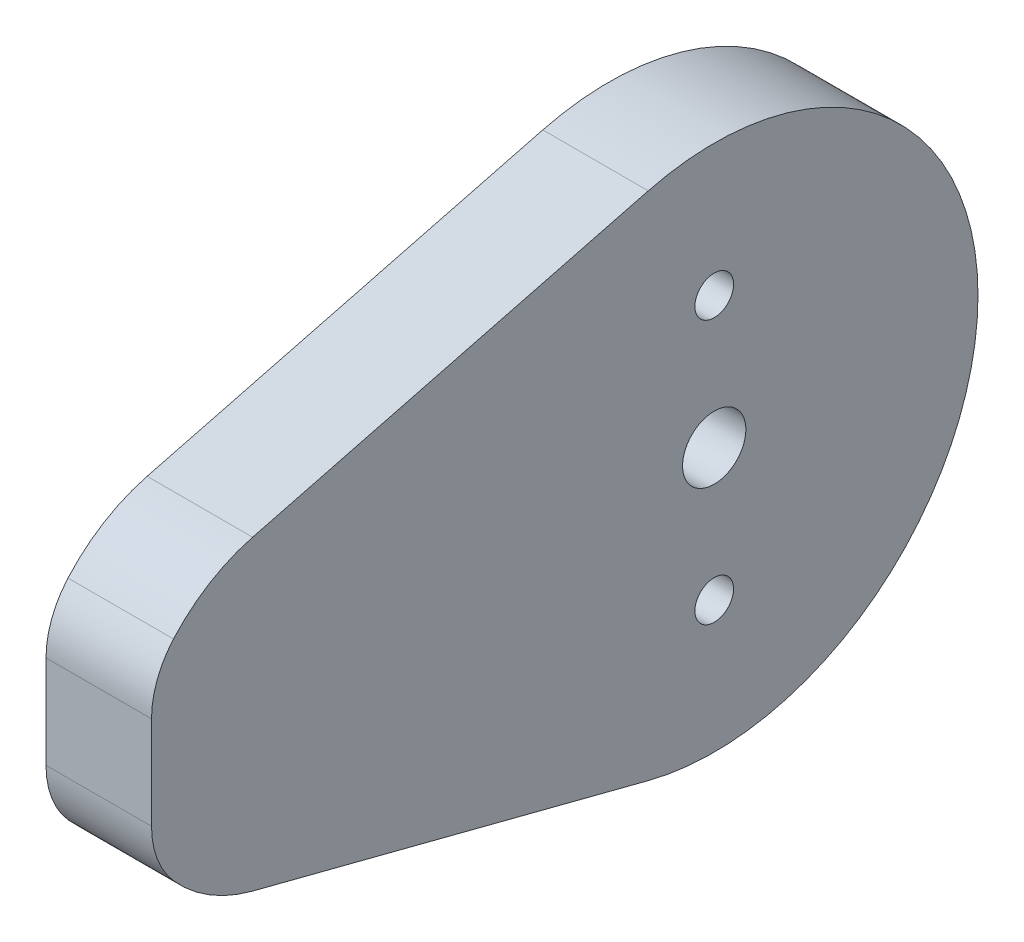
SolidWorks part; units mm, degrees
ref_plane "Plan de face" through (0, 0, 0) normal (0, 0, 1) x (1, 0, 0)
ref_plane "Plan de dessus" through (0, 0, 0) normal (0, 1, 0) x (1, 0, 0)
ref_plane "Plan de droite" through (0, 0, 0) normal (1, 0, 0) x (0, 0, -1)
sketch "Esquisse1" plane through (0, 0, 0) normal (1, 0, 0) x (0, 0, -1)
  line L0 (61.1, -8.9434) -> (61.1, 59.3647) construction
  line L1 (66.1354, 33.9) -> (52.8313, 33.9) construction
  line L2 (37.1, 3.4262) -> (37.1, 59.3647) construction
  line L3 (29.1, 44.0458) -> (29.1, 38.7542)
  line L4 (82, -8.9434) -> (82, 76.684) construction
  line L6 (34.85, 32.6858) -> (57.35, 26.8763)
  line L7 (94.833, 41.4) -> (22.7655, 41.4) construction
  line L8 (34.85, 50.1142) -> (57.35, 55.9237)
  line L26 (29.1, 58.1981) -> (29.1, -8.9434) construction
  circle A0 centre (61.1, 33.9) radius 1.1
  circle A1 centre (61.1, 48.9) radius 1.1
  arc A2 (57.35, 26.8763) -> (57.35, 55.9237) centre (61.1, 41.4) ccw
  arc A3 (30.35, 35.4471) -> (34.85, 32.6858) centre (37.1, 41.4) ccw
  arc A4 (34.85, 50.1142) -> (30.35, 47.3529) centre (37.1, 41.4) ccw
  arc A5 (30.35, 47.3529) -> (29.1, 44.0458) centre (34.1, 44.0458) ccw
  arc A6 (29.1, 38.7542) -> (30.35, 35.4471) centre (34.1, 38.7542) ccw
  circle A7 centre (61.1, 41.4) radius 1.8
  point P21 (29.1, 37.2769)
  dimension "D3" = 7.5
  dimension "D1" = 32
  dimension "D4" = 5
  dimension "D2" = 20.9
extrude "Boss.-Extru.1" add sketch "Esquisse1" along normal blind 6
